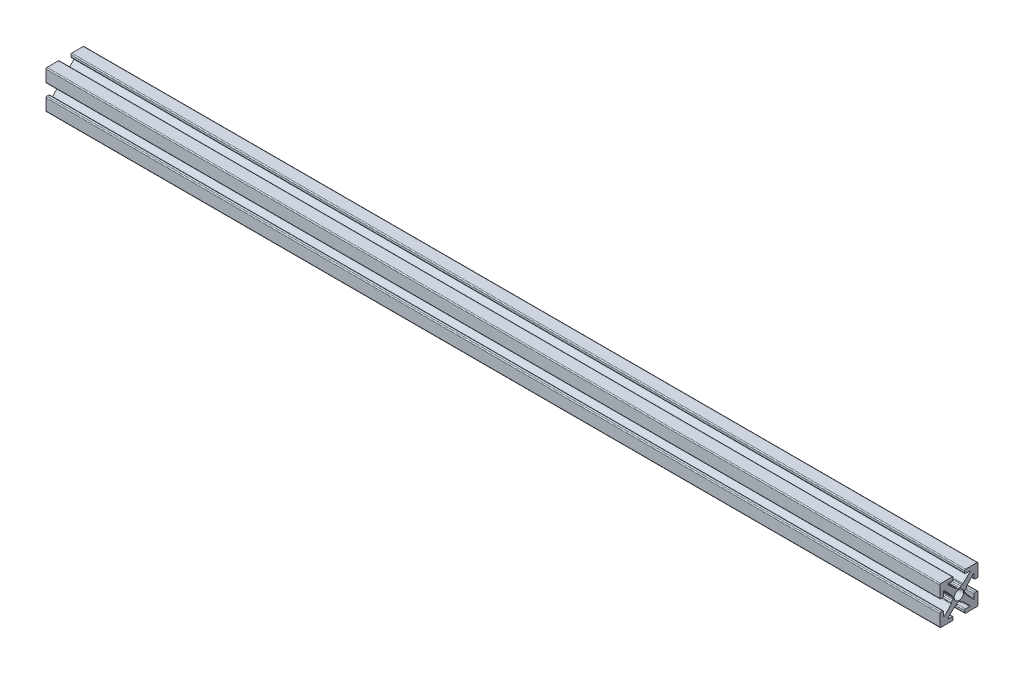
SolidWorks part; units mm, degrees
material "Acciaio in lega fuso"
ref_plane "Front Plane" through (0, 0, 0) normal (0, 0, 1) x (1, 0, 0)
ref_plane "Top Plane" through (0, 0, 0) normal (0, 1, 0) x (1, 0, 0)
ref_plane "Right Plane" through (0, 0, 0) normal (1, 0, 0) x (0, 0, -1)
sketch "Sketch1" plane through (0, 0, 0) normal (1, 0, 0) x (0, 0, -1)
  line L0 (0, 0) -> (0, 1.4986) construction
  line L1 (-0.2413, 1.4986) -> (0.2413, 1.4986)
  line L2 (5.0038, 1.7526) -> (5.0038, 4.7498)
  line L3 (0.7493, 2.0066) -> (0.8899, 2.0066)
  line L4 (1.0639, 2.0756) -> (2.8908, 3.7937)
  line L5 (2.8038, 4.0132) -> (1.7526, 4.0132)
  line L6 (1.4986, 4.2672) -> (1.4986, 4.7498)
  line L7 (1.7526, 5.0038) -> (4.7498, 5.0038)
  line L8 (5.0038, 5.0038) -> (0, 0) construction
  line L9 (0, 0) -> (8.6271, 0) construction
  line L10 (0, 0) -> (0, 5.0038) construction
  line L11 (4.2672, 1.4986) -> (4.7498, 1.4986)
  line L12 (4.0132, 2.8038) -> (4.0132, 1.7526)
  line L13 (2.0756, 1.0639) -> (3.7937, 2.8908)
  line L14 (2.0066, 0.7493) -> (2.0066, 0.8899)
  line L15 (1.4986, -0.2413) -> (1.4986, 0.2413)
  line L16 (0, 0) -> (1.4986, 0) construction
  line L17 (-0.2413, -1.4986) -> (0.2413, -1.4986)
  line L18 (0.7493, -2.0066) -> (0.8899, -2.0066)
  line L19 (1.0639, -2.0756) -> (2.8908, -3.7937)
  line L20 (2.8038, -4.0132) -> (1.7526, -4.0132)
  line L21 (1.4986, -4.2672) -> (1.4986, -4.7498)
  line L22 (1.7526, -5.0038) -> (4.7498, -5.0038)
  line L23 (5.0038, -1.7526) -> (5.0038, -4.7498)
  line L24 (4.2672, -1.4986) -> (4.7498, -1.4986)
  line L25 (4.0132, -2.8038) -> (4.0132, -1.7526)
  line L26 (2.0756, -1.0639) -> (3.7937, -2.8908)
  line L27 (2.0066, -0.7493) -> (2.0066, -0.8899)
  line L28 (-0.7493, 2.0066) -> (-0.8899, 2.0066)
  line L29 (-1.0639, 2.0756) -> (-2.8908, 3.7937)
  line L30 (-2.8038, 4.0132) -> (-1.7526, 4.0132)
  line L31 (-1.4986, 4.2672) -> (-1.4986, 4.7498)
  line L32 (-1.7526, 5.0038) -> (-4.7498, 5.0038)
  line L33 (-5.0038, 1.7526) -> (-5.0038, 4.7498)
  line L34 (-4.2672, 1.4986) -> (-4.7498, 1.4986)
  line L35 (-4.0132, 2.8038) -> (-4.0132, 1.7526)
  line L36 (-2.0756, 1.0639) -> (-3.7937, 2.8908)
  line L37 (-2.0066, 0.7493) -> (-2.0066, 0.8899)
  line L38 (-1.4986, -0.2413) -> (-1.4986, 0.2413)
  line L39 (-2.0066, -0.7493) -> (-2.0066, -0.8899)
  line L40 (-2.0756, -1.0639) -> (-3.7937, -2.8908)
  line L41 (-4.0132, -2.8038) -> (-4.0132, -1.7526)
  line L42 (-4.2672, -1.4986) -> (-4.7498, -1.4986)
  line L43 (-5.0038, -1.7526) -> (-5.0038, -4.7498)
  line L44 (-1.7526, -5.0038) -> (-4.7498, -5.0038)
  line L45 (-1.4986, -4.2672) -> (-1.4986, -4.7498)
  line L46 (-2.8038, -4.0132) -> (-1.7526, -4.0132)
  line L47 (-1.0639, -2.0756) -> (-2.8908, -3.7937)
  line L48 (-0.7493, -2.0066) -> (-0.8899, -2.0066)
  arc A0 (2.8908, 3.7937) -> (2.8038, 4.0132) centre (2.8038, 3.8862) ccw
  arc A1 (0.4953, 1.7526) -> (0.7493, 2.0066) centre (0.7493, 1.7526) cw
  arc A2 (0.8899, 2.0066) -> (1.0639, 2.0756) centre (0.8899, 2.2606) ccw
  arc A3 (1.7526, 4.0132) -> (1.4986, 4.2672) centre (1.7526, 4.2672) cw
  arc A4 (1.4986, 4.7498) -> (1.7526, 5.0038) centre (1.7526, 4.7498) cw
  arc A5 (0.2413, 1.4986) -> (0.4953, 1.7526) centre (0.2413, 1.7526) ccw
  arc A6 (4.7498, 1.4986) -> (5.0038, 1.7526) centre (4.7498, 1.7526) ccw
  arc A7 (4.0132, 1.7526) -> (4.2672, 1.4986) centre (4.2672, 1.7526) ccw
  arc A8 (3.7937, 2.8908) -> (4.0132, 2.8038) centre (3.8862, 2.8038) cw
  arc A9 (2.0066, 0.8899) -> (2.0756, 1.0639) centre (2.2606, 0.8899) cw
  arc A10 (1.7526, 0.4953) -> (2.0066, 0.7493) centre (1.7526, 0.7493) ccw
  arc A11 (1.4986, 0.2413) -> (1.7526, 0.4953) centre (1.7526, 0.2413) cw
  arc A12 (0.2413, -1.4986) -> (0.4953, -1.7526) centre (0.2413, -1.7526) cw
  arc A13 (0.4953, -1.7526) -> (0.7493, -2.0066) centre (0.7493, -1.7526) ccw
  arc A14 (0.8899, -2.0066) -> (1.0639, -2.0756) centre (0.8899, -2.2606) cw
  arc A15 (2.8908, -3.7937) -> (2.8038, -4.0132) centre (2.8038, -3.8862) cw
  arc A16 (1.7526, -4.0132) -> (1.4986, -4.2672) centre (1.7526, -4.2672) ccw
  arc A17 (1.4986, -4.7498) -> (1.7526, -5.0038) centre (1.7526, -4.7498) ccw
  arc A18 (4.7498, -1.4986) -> (5.0038, -1.7526) centre (4.7498, -1.7526) cw
  arc A19 (4.0132, -1.7526) -> (4.2672, -1.4986) centre (4.2672, -1.7526) cw
  arc A20 (3.7937, -2.8908) -> (4.0132, -2.8038) centre (3.8862, -2.8038) ccw
  arc A21 (2.0066, -0.8899) -> (2.0756, -1.0639) centre (2.2606, -0.8899) ccw
  arc A22 (1.7526, -0.4953) -> (2.0066, -0.7493) centre (1.7526, -0.7493) cw
  arc A23 (1.4986, -0.2413) -> (1.7526, -0.4953) centre (1.7526, -0.2413) ccw
  arc A24 (-0.2413, 1.4986) -> (-0.4953, 1.7526) centre (-0.2413, 1.7526) cw
  arc A25 (-0.4953, 1.7526) -> (-0.7493, 2.0066) centre (-0.7493, 1.7526) ccw
  arc A26 (-0.8899, 2.0066) -> (-1.0639, 2.0756) centre (-0.8899, 2.2606) cw
  arc A27 (-2.8908, 3.7937) -> (-2.8038, 4.0132) centre (-2.8038, 3.8862) cw
  arc A28 (-1.7526, 4.0132) -> (-1.4986, 4.2672) centre (-1.7526, 4.2672) ccw
  arc A29 (-1.4986, 4.7498) -> (-1.7526, 5.0038) centre (-1.7526, 4.7498) ccw
  arc A30 (-4.7498, 1.4986) -> (-5.0038, 1.7526) centre (-4.7498, 1.7526) cw
  arc A31 (-4.0132, 1.7526) -> (-4.2672, 1.4986) centre (-4.2672, 1.7526) cw
  arc A32 (-3.7937, 2.8908) -> (-4.0132, 2.8038) centre (-3.8862, 2.8038) ccw
  arc A33 (-2.0066, 0.8899) -> (-2.0756, 1.0639) centre (-2.2606, 0.8899) ccw
  arc A34 (-1.7526, 0.4953) -> (-2.0066, 0.7493) centre (-1.7526, 0.7493) cw
  arc A35 (-1.4986, 0.2413) -> (-1.7526, 0.4953) centre (-1.7526, 0.2413) ccw
  arc A36 (-1.4986, -0.2413) -> (-1.7526, -0.4953) centre (-1.7526, -0.2413) cw
  arc A37 (-1.7526, -0.4953) -> (-2.0066, -0.7493) centre (-1.7526, -0.7493) ccw
  arc A38 (-2.0066, -0.8899) -> (-2.0756, -1.0639) centre (-2.2606, -0.8899) cw
  arc A39 (-3.7937, -2.8908) -> (-4.0132, -2.8038) centre (-3.8862, -2.8038) cw
  arc A40 (-4.0132, -1.7526) -> (-4.2672, -1.4986) centre (-4.2672, -1.7526) ccw
  arc A41 (-4.7498, -1.4986) -> (-5.0038, -1.7526) centre (-4.7498, -1.7526) ccw
  arc A42 (-1.4986, -4.7498) -> (-1.7526, -5.0038) centre (-1.7526, -4.7498) cw
  arc A43 (-1.7526, -4.0132) -> (-1.4986, -4.2672) centre (-1.7526, -4.2672) cw
  arc A44 (-2.8908, -3.7937) -> (-2.8038, -4.0132) centre (-2.8038, -3.8862) ccw
  arc A45 (-0.8899, -2.0066) -> (-1.0639, -2.0756) centre (-0.8899, -2.2606) ccw
  arc A46 (-0.4953, -1.7526) -> (-0.7493, -2.0066) centre (-0.7493, -1.7526) cw
  arc A47 (-0.2413, -1.4986) -> (-0.4953, -1.7526) centre (-0.2413, -1.7526) ccw
  arc A48 (-4.7498, 5.0038) -> (-5.0038, 4.7498) centre (-4.7498, 4.7498) ccw
  arc A49 (-5.0038, -4.7498) -> (-4.7498, -5.0038) centre (-4.7498, -4.7498) ccw
  arc A50 (4.7498, -5.0038) -> (5.0038, -4.7498) centre (4.7498, -4.7498) ccw
  arc A51 (4.7498, 5.0038) -> (5.0038, 4.7498) centre (4.7498, 4.7498) cw
  point P14 (3.1242, 4.0132)
  point P19 (0.9906, 2.0066)
  point P150 (0, -1.4986)
  point P152 (-5.0038, 5.0038)
  point P155 (-5.0038, -5.0038)
  point P158 (5.0038, -5.0038)
  dimension "D10" = 0.127
  dimension "D11" = 0.254
  dimension "D2" = 0.254
  dimension "D1" = 10.0076
  dimension "D3" = 2.9972
  dimension "D4" = 0.508
  dimension "D5" = 2.9972
  dimension "D6" = 0.9906
  dimension "D7" = 1.6256
  dimension "D8" = 1.9812
  dimension "D9" = 0.9906
extrude "Estrusione-Estrusione1" add sketch "Sketch1" along normal blind 234.4674 contours L36 A32 L35 A31 L34 A30 L33 A48 L32 A29 L31 A28 L30 A27 L29 A26 L28 A25 A24 L1 A5 A1 L3 A2 L4 A0 L5 A3 L6 A4 L7 A51 L2 A6 L11 A7 L12 A8 L13 A9 L14 A10 A11 L15 A23 A22 L27 A21 L26 A20 L25 A19 L24 A18 L23 A50 L22 A17 L21 A16 L20 A15 L19 A14 L18 A13 A12 L17 A47 A46 L48 A45 L47 A44 L46 A43 L45 A42 L44 A49 L43 A41 L42 A40 L41 A39 L40 A38 L39 A37 A36 L38 A35 A34 L37 A33
hole_wizard "Foro filettato M3x0.5-1" positions "Schizzo2" profile "Schizzo1" tap size "M3x0.5" standard "Ansi Metric" end condition through all
sketch "Schizzo2" plane through (0, 0, 0) normal (-1, 0, 0) x (0, 0, 1)
  point P0 (0, 0)
sketch "Schizzo1" plane through (0, 0, 0) normal (0, 1, 0) x (0, 0, 1)
  line L0 (0, 0) -> (0, 234.4674)
  line L1 (0, 234.4674) -> (1.25, 234.4674)
  line L2 (1.25, 234.4674) -> (1.25, 0)
  line L5 (1.25, 0) -> (0, 0)
  line L11 (0, -6.35) -> (0, 107.95) construction
  dimension "Thread Major Dia." = 2.5
  dimension "Thru Tap Drill Depth" = 234.4674
